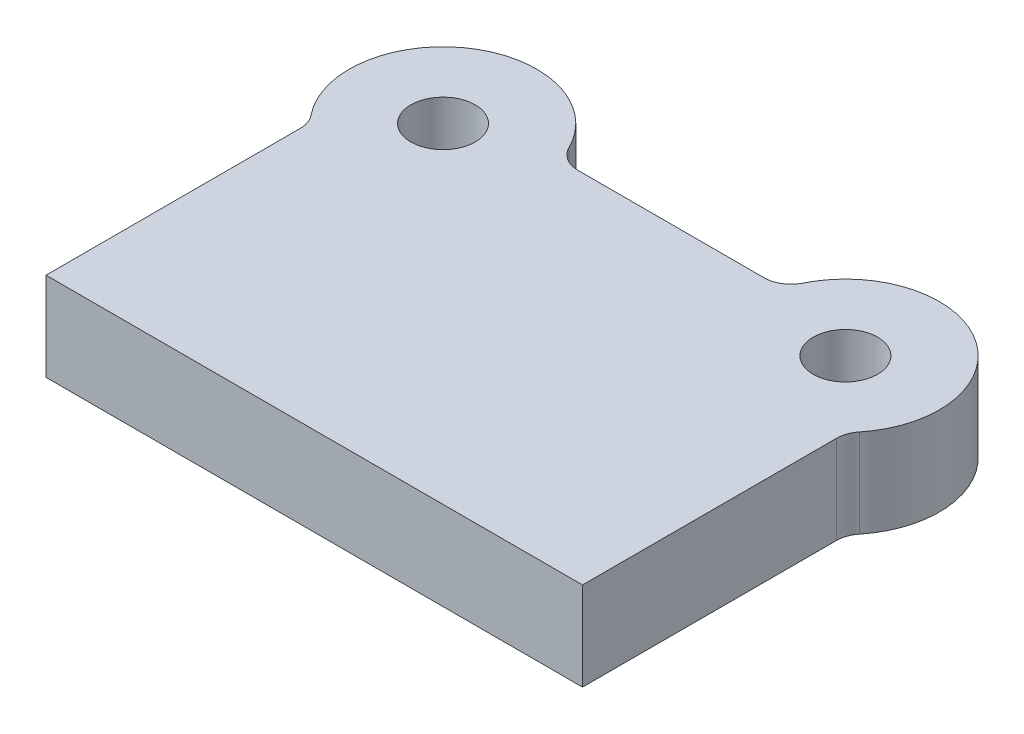
SolidWorks part; units mm, degrees
ref_plane "Front Plane" through (0, 0, 0) normal (0, 0, 1) x (1, 0, 0)
ref_plane "Top Plane" through (0, 0, 0) normal (0, 1, 0) x (1, 0, 0)
ref_plane "Right Plane" through (0, 0, 0) normal (1, 0, 0) x (0, 0, -1)
sketch "Sketch1" plane through (0, 0, 0) normal (0, 1, 0) x (1, 0, 0)
  line L0 (100, 0) -> (-100, 0)
  line L1 (-100, 0) -> (-100, 98.5051)
  line L2 (0, 0) -> (0, 133) construction
  line L3 (41.459, 133) -> (-41.459, 133)
  line L4 (100, 0) -> (100, 98.5051)
  arc A0 (-41.459, 133) -> (-100, 98.5051) centre (-75, 123) ccw
  circle A1 centre (-75, 123) radius 12
  circle A2 centre (75, 123) radius 12
  arc A3 (41.459, 133) -> (100, 98.5051) centre (75, 123) cw
  dimension "D2" = 70
  dimension "D3" = 24
  dimension "D1" = 123
  dimension "D4" = 200
  dimension "D5" = 150
  dimension "D6" = 133
extrude "Boss-Extrude1" add sketch "Sketch1" along normal blind 33
fillet "Fillet1" radius 10 4 edges at (-100, 16.5, -98.5051) (100, 16.5, -98.5051) (-41.459, 16.5, -133) (41.459, 16.5, -133)
